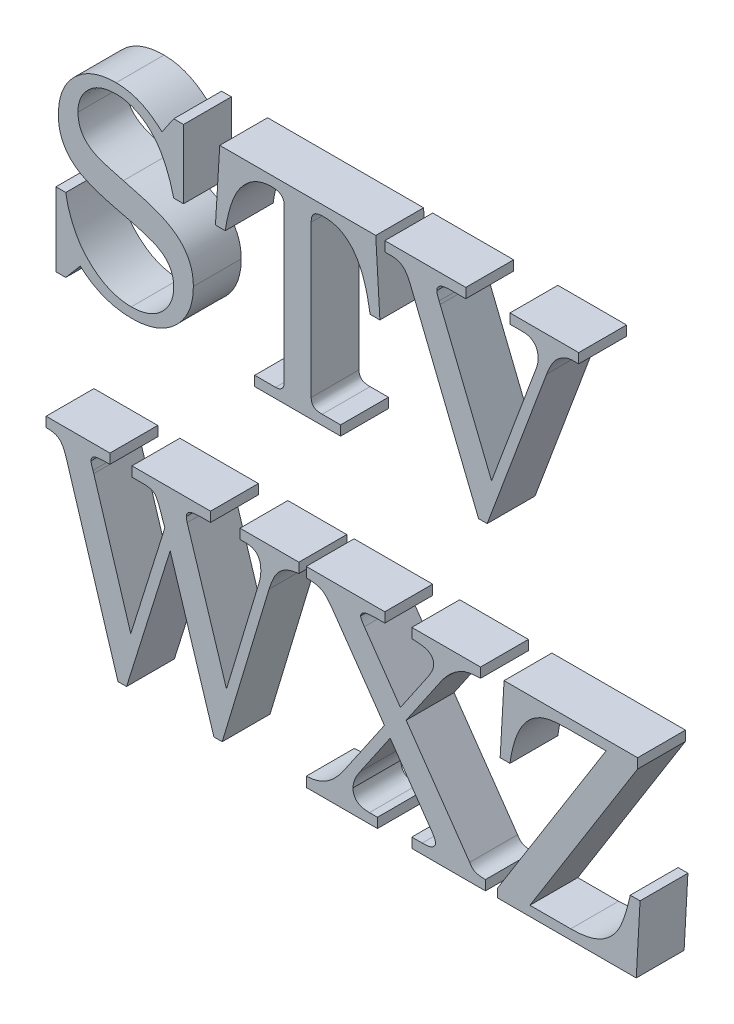
SolidWorks part; units mm, degrees
ref_plane "Plan de face" through (0, 0, 0) normal (0, 0, 1) x (1, 0, 0)
ref_plane "Plan de dessus" through (0, 0, 0) normal (0, 1, 0) x (1, 0, 0)
ref_plane "Plan de droite" through (0, 0, 0) normal (1, 0, 0) x (0, 0, -1)
sketch "Esquisse1" plane through (0, 0, 0) normal (0, 0, 1) x (1, 0, 0)
  text T0 "STV\r\nWXZ\r\n" font "Century Schoolbook" height 40
extrude "Boss.-Extru.1" add sketch "Esquisse1" along normal blind 10
